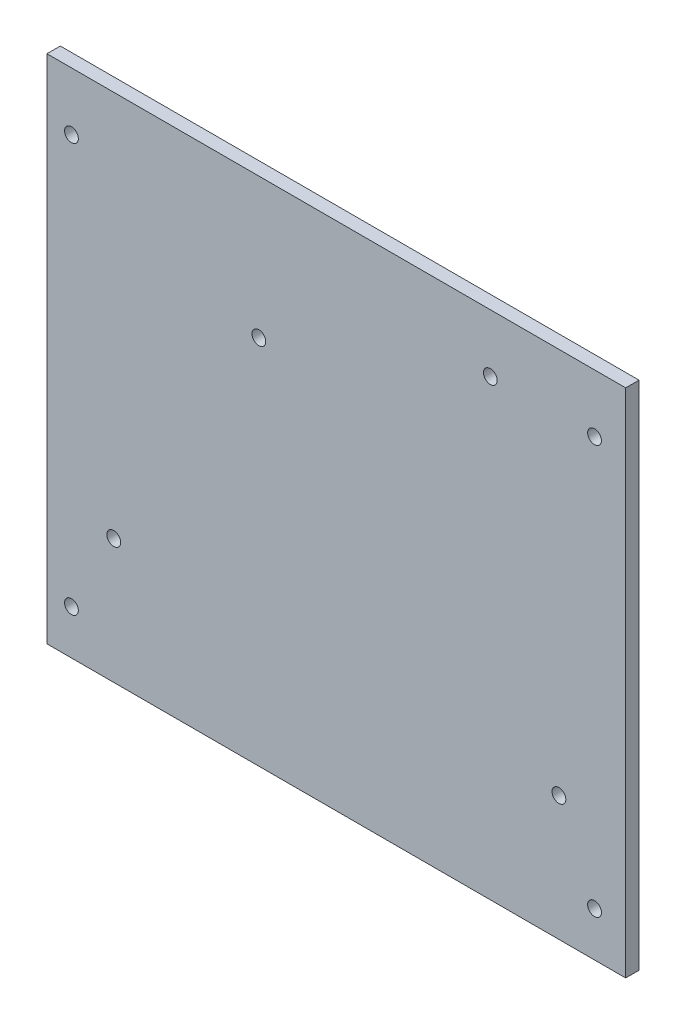
SolidWorks part; units mm, degrees
ref_plane "Front" through (0, 0, 0) normal (0, 0, 1) x (1, 0, 0)
ref_plane "Top" through (0, 0, 0) normal (0, 1, 0) x (1, 0, 0)
ref_plane "Right" through (0, 0, 0) normal (1, 0, 0) x (0, 0, -1)
sketch "Sketch1" plane through (0, 0, 0) normal (0, 0, 1) x (1, 0, 0)
  line L0 (65, 0) -> (0, 0) construction
  line L1 (-65, -57.4) -> (65, -57.4)
  line L2 (-65, -57.4) -> (-65, 57.4)
  line L3 (-65, 57.4) -> (65, 57.4)
  line L4 (65, -57.4) -> (65, 57.4)
  line L5 (-65, -57.4) -> (65, 57.4) construction
  line L6 (-65, 57.4) -> (65, -57.4) construction
  circle A0 centre (-59.5, 44.4) radius 1.55
  circle A1 centre (58, 44.4) radius 1.55
  circle A4 centre (58, -47.4) radius 1.55
  circle A5 centre (-59.5, -47.4) radius 1.55
  point P0 (0, 0)
  dimension "D3" = 3.1
  dimension "D4" = 3.1
  dimension "D5" = 13
  dimension "D6" = 5.5
  dimension "D7" = 7
  dimension "D8" = 3.1
  dimension "D9" = 3.1
  dimension "D10" = 10
  dimension "D1" = 114.8
  dimension "D2" = 130
extrude "Boss-Extrude1" add sketch "Sketch1" along normal blind 3
sketch "Sketch2" plane through (0, 0, 3) normal (0, 0, 1) x (1, 0, 0)
  line L1 (-44.5, -37.5) -> (44.5, -37.5)
  line L2 (-44.5, -37.5) -> (-44.5, 34.5)
  line L3 (-44.5, 34.5) -> (44.5, 34.5)
  line L4 (44.5, -37.5) -> (44.5, 34.5)
  line L5 (-44.5, -37.5) -> (44.5, 34.5) construction
  line L6 (-44.5, 34.5) -> (44.5, -37.5) construction
  point P0 (0, -1.5)
  dimension "D1" = 72
  dimension "D2" = 89
  dimension "D3" = 1.5
extrude "Boss-Extrude2" [suppressed] add sketch "Sketch2" along normal blind 4
sketch "Sketch3" plane through (0, 0, 0) normal (0, 0, -1) x (-1, 0, 0)
  line L0 (65, -57.4) -> (-65, -57.4) construction
  circle A0 centre (-50, -29.4) radius 1.55
  circle A1 centre (50, -29.4) radius 1.55
  dimension "D1" = 3.1
  dimension "D2" = 3.1
  dimension "D4" = 100
  dimension "D3" = 28
  dimension "D5" = 50
extrude "Cut-Extrude1" cut sketch "Sketch3" against normal up to next
sketch "Sketch4" plane through (0, 0, 0) normal (0, 0, -1) x (-1, 0, 0)
  line L0 (-65, 57.4) -> (65, 57.4) construction
  line L1 (-65, -57.4) -> (-65, 57.4) construction
  line L2 (65, 57.4) -> (65, -57.4) construction
  circle A0 centre (-34.6, 44.4) radius 1.55
  circle A1 centre (17.4, 25.96) radius 1.55
  dimension "D1" = 3.1
  dimension "D2" = 3.1
  dimension "D3" = 13
  dimension "D4" = 30.4
  dimension "D5" = 47.6
  dimension "D6" = 31.44
extrude "Cut-Extrude2" cut sketch "Sketch4" against normal up to next
